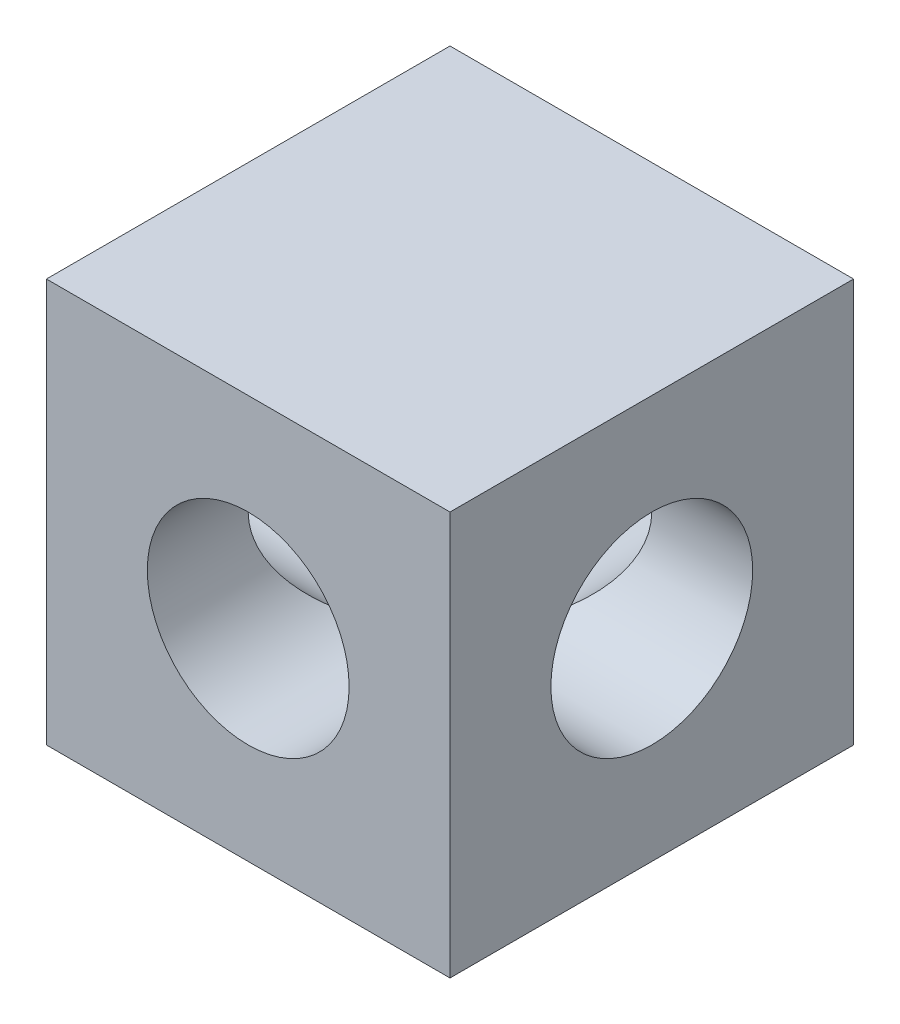
SolidWorks part; units mm, degrees
ref_plane "Front" through (0, 0, 0) normal (0, 0, 1) x (1, 0, 0)
ref_plane "Top" through (0, 0, 0) normal (0, 1, 0) x (-1, 0, 0)
ref_plane "Right" through (0, 0, 0) normal (1, 0, 0) x (0, 0, -1)
sketch "Sketch1" plane through (0, 0, 0) normal (0, 0, 1) x (1, 0, 0)
  line L0 (-9.525, -9.525) -> (9.525, -9.525)
  line L1 (-9.525, -9.525) -> (-9.525, 9.525)
  line L2 (9.525, 9.525) -> (-9.525, 9.525)
  line L3 (9.525, 9.525) -> (9.525, -9.525)
  line L4 (9.525, 9.525) -> (-9.525, -9.525) construction
  circle A0 centre (0, 0) radius 4.7625
extrude "Base-Extrude" add sketch "Sketch1" along normal mid plane 19.05
sketch "Sketch3" plane through (9.525, 0, 0) normal (1, 0, 0) x (0, 0, -1)
  circle A0 centre (0, 0) radius 4.7625
extrude "Cut-Extrude1" cut sketch "Sketch3" against normal through all
